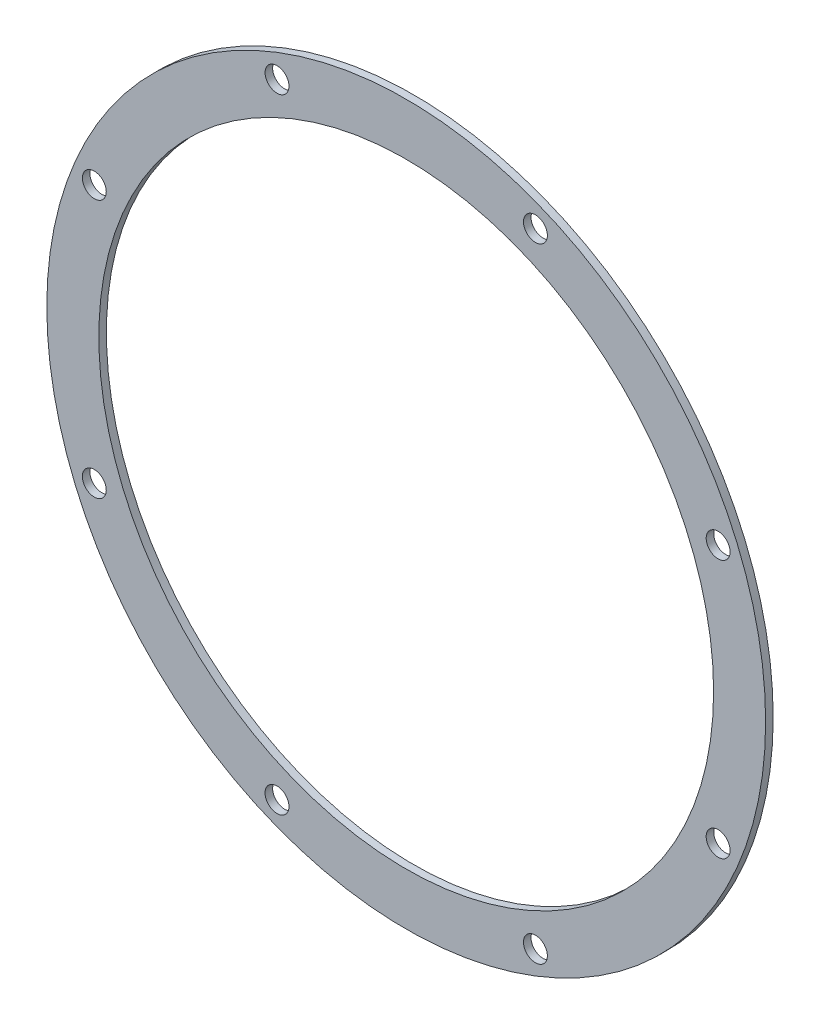
SolidWorks part; units mm, degrees
ref_plane "Front Plane" through (0, 0, 0) normal (0, 0, 1) x (1, 0, 0)
ref_plane "Top Plane" through (0, 0, 0) normal (0, 1, 0) x (1, 0, 0)
ref_plane "Right Plane" through (0, 0, 0) normal (1, 0, 0) x (0, 0, -1)
sketch "Sketch1" plane through (0, 0, 0) normal (0, 0, 1) x (1, 0, 0)
  circle A0 centre (0, 0) radius 65
  circle A1 centre (0, 0) radius 76
  dimension "D1" = 152
  dimension "D2" = 130
extrude "Boss-Extrude1" add sketch "Sketch1" along normal blind 1.6
sketch "Sketch2" plane through (0, 0, 1.6) normal (0, 0, 1) x (1, 0, 0)
  line L7 (27.3185, -65.9527) -> (65.9527, -27.3185) construction
  line L8 (65.9527, -27.3185) -> (65.9527, 27.3185) construction
  line L9 (65.9527, 27.3185) -> (27.3185, 65.9527) construction
  line L10 (27.3185, 65.9527) -> (-27.3185, 65.9527) construction
  line L11 (-27.3185, 65.9527) -> (-65.9527, 27.3185) construction
  line L12 (-65.9527, 27.3185) -> (-65.9527, -27.3185) construction
  line L13 (-65.9527, -27.3185) -> (-27.3185, -65.9527) construction
  line L14 (-27.3185, -65.9527) -> (27.3185, -65.9527) construction
  circle A0 centre (0, 0) radius 65.9527 construction
  point P18 (-27.3185, 65.9527)
  point P19 (27.3185, 65.9527)
  point P20 (65.9527, 27.3185)
  point P21 (65.9527, -27.3185)
  point P22 (27.3185, -65.9527)
  point P23 (-27.3185, -65.9527)
  point P25 (-65.9527, -27.3185)
  point P26 (-65.9527, 27.3185)
  dimension "D1" = 142.7734
hole_wizard "#8 (0.199) Diameter Hole1" positions "3DSketch1" profile "Sketch3" hole size "#8" standard "ANSI Inch"
sketch3d "3DSketch1"
  point P21 (-27.3185, 65.9527, 1.6)
  point P24 (27.3185, 65.9527, 1.6)
  point P27 (65.9527, 27.3185, 1.6)
  point P30 (65.9527, -27.3185, 1.6)
  point P33 (27.3185, -65.9527, 1.6)
  point P36 (-27.3185, -65.9527, 1.6)
  point P39 (-65.9527, -27.3185, 1.6)
  point P42 (-65.9527, 27.3185, 1.6)
  point P45 (0, 0, 0)
  point P46 (0, 0, 0)
  point P47 (0, 0, 0)
  point P48 (0, 0, 0)
  point P49 (0, 0, 0)
  point P50 (0, 0, 0)
sketch "Sketch3" plane through (-27.3185, 65.9527, 1.6) normal (1, 0, 0) x (0, -1, 0)
  line L0 (0, 0) -> (0, 10)
  line L1 (0, 10) -> (2.5273, 8.4814)
  line L2 (2.5273, 8.4814) -> (2.5273, 0)
  line L5 (2.5273, 0) -> (0, 0)
  line L10 (0, 10) -> (-2.5273, 8.4814) construction
  line L11 (0, -6.35) -> (0, 107.95) construction
  dimension "Hole Dia." = 5.0546
  dimension "Hole Depth" = 10
  dimension "Drill Angle" = 118
